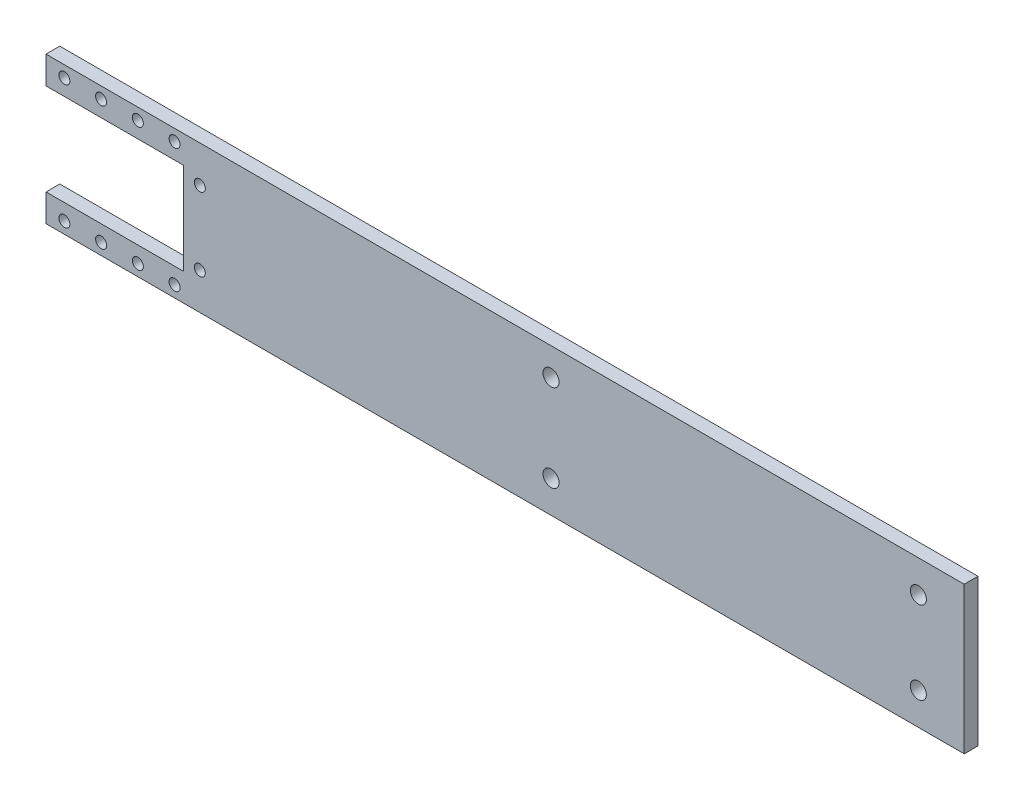
SolidWorks part; units mm, degrees
ref_plane "Front plane" through (0, 0, 0) normal (0, 0, 1) x (1, 0, 0)
ref_plane "Top plane" through (0, 0, 0) normal (0, 1, 0) x (1, 0, 0)
ref_plane "Plan de droite" through (0, 0, 0) normal (1, 0, 0) x (0, 0, -1)
sketch "Esquisse1" plane through (0, 0, 0) normal (0, 0, 1) x (1, 0, 0)
  line L0 (-12.25, 10) -> (12.25, 10)
  line L1 (19.6775, 17) -> (48.9006, -4.024)
  line L2 (48.9006, -4.024) -> (67.9013, -77.094)
  line L3 (67.9013, -77.094) -> (72.5958, -84.7726)
  line L4 (72.5958, -84.7726) -> (62.3576, -91.032)
  line L5 (62.3576, -91.032) -> (46.2854, -78.3067)
  line L6 (46.2854, -78.3067) -> (46.7112, -66.8067)
  line L7 (46.7112, -66.8067) -> (20.3918, -26.6658)
  line L8 (-12.25, 10) -> (-12.25, -10)
  line L9 (-12.25, -10) -> (12.25, -10)
  line L10 (12.25, 10) -> (12.25, -10)
  line L11 (-17.75, 10) -> (-17.75, -10)
  line L12 (-12.25, 10) -> (12.25, -10) construction
  line L13 (12.25, 10) -> (-12.25, -10) construction
  line L14 (-17.75, 10) -> (-17.75, 17)
  line L15 (-12.25, -10) -> (-17.75, -10)
  line L16 (-12.25, 10) -> (-17.75, 10)
  line L17 (44.278, -14.0621) -> (55.6029, -57.6137)
  line L18 (55.6029, -57.6137) -> (51.0231, -60.6166)
  line L19 (51.0231, -60.6166) -> (28.8161, -26.7478)
  line L20 (28.8161, -26.7478) -> (44.278, -14.0621)
  line L21 (23.25, 5.9738) -> (23.25, -19.0262)
  line L22 (23.25, -19.0262) -> (39.4851, -5.7062)
  line L23 (39.4851, -5.7062) -> (23.25, 5.9738)
  line L24 (19.6775, 17) -> (20.3918, -26.6658)
  line L25 (-1000, 0) -> (49000, 0) construction
  line L26 (-17.75, 17) -> (12.25, 17)
  line L27 (12.25, 17) -> (12.25, 10)
  line L28 (12.25, -10) -> (12.25, -16)
  line L29 (12.25, -16) -> (-17.75, -16)
  line L30 (-17.75, -16) -> (-17.75, -10)
  line L31 (19.6775, 17) -> (12.25, 17)
  line L32 (6.25, -10) -> (6.25, -16)
  line L33 (6.25, -16) -> (20.3918, -26.6658)
  point P17 (10.25, -13.5)
  point P18 (2.25, -13.5)
  point P25 (-5.75, -13.5)
  point P26 (-13.75, -13.5)
  point P27 (10.25, 13.5)
  point P28 (2.25, 13.5)
  point P29 (-5.75, 13.5)
  point P30 (-13.75, 13.5)
  point P31 (15.75, -8)
  point P32 (15.75, 8)
  dimension "D2" = 75.5
  dimension "D3" = 36
  dimension "D4" = 9
  dimension "D5" = 12
  dimension "D6" = 20.5
  dimension "D7" = 11.5
  dimension "D8" = 48
  dimension "D9" = 7
  dimension "D10" = 7
  dimension "D11" = 9.5
  dimension "D12" = 20
  dimension "D13" = 24.5
  dimension "D14" = 8
  dimension "D15" = 27
  dimension "D16" = 3.5
  dimension "D17" = 2
  dimension "D18" = 3.5
  dimension "D19" = 2
  dimension "D20" = 5.5
  dimension "D21" = 8
  dimension "D22" = 8
  dimension "D23" = 8
  dimension "D24" = 8
  dimension "D25" = 8
  dimension "D26" = 16
  dimension "D27" = 6
  dimension "D28" = 7
  dimension "D29" = 4
  dimension "D30" = 11
  dimension "D31" = 20
  dimension "D32" = 40.5
  dimension "D33" = 45
  dimension "D34" = 20
  dimension "D35" = 21
  dimension "D36" = 25
sketch "Sketch1" plane through (0, 0, 0) normal (0, 0, 1) x (1, 0, 0)
  line L13 (-17.75, 16) -> (182.25, 16)
  line L14 (-17.75, -16) -> (-17.75, -10)
  line L17 (-17.75, -10) -> (12.25, -10)
  line L18 (-17.75, 10) -> (12.25, 10)
  line L21 (-17.75, 10) -> (-17.75, 16)
  line L22 (182.25, 16) -> (182.25, -16)
  line L23 (182.25, -16) -> (-17.75, -16)
  line L24 (12.25, 10) -> (12.25, -10)
  dimension "D1" = 200
  dimension "D2" = 6
  dimension "D3" = 30
  dimension "D4" = 20
  dimension "D5" = 6
  dimension "D6" = 10
extrude "Boss-Extrude1" add sketch "Sketch1" along normal blind 3 separate body contours L13 L22 L23 L14 L17 L24 L18 L21
sketch "Sketch2" plane through (0, 0, 3) normal (0, 0, 1) x (1, 0, 0)
  line L0 (-17.168, 0) -> (29.6324, 0) construction
  point P0 (-13.75, 13.5)
  point P2 (-5.75, 13.5)
  point P4 (2.25, 13.5)
  point P6 (10.25, 13.5)
  point P8 (15.75, 8)
  point P13 (15.75, -8)
  point P14 (10.25, -13.5)
  point P15 (2.25, -13.5)
  point P16 (-5.75, -13.5)
  point P17 (-13.75, -13.5)
  dimension "D1" = 8
  dimension "D2" = 8
  dimension "D3" = 8
  dimension "D4" = 13.5
  dimension "D5" = 5.5
  dimension "D6" = 8
hole_wizard "M2 Clearance Hole1" positions "Sketch4" profile "Sketch3" hole size "M2" standard "ISO" end condition through all
sketch "Sketch4" plane through (0, 0, 3) normal (0, 0, 1) x (1, 0, 0)
  point P0 (-13.75, 13.5)
  point P3 (-5.75, 13.5)
  point P6 (2.25, 13.5)
  point P9 (10.25, 13.5)
  point P12 (15.75, 8)
  point P15 (15.75, -8)
  point P18 (10.25, -13.5)
  point P21 (2.25, -13.5)
  point P24 (-5.75, -13.5)
  point P27 (-13.75, -13.5)
sketch "Sketch3" plane through (-13.75, 13.5, 3) normal (1, 0, 0) x (0, -1, 0)
  line L0 (0, 0) -> (0, 3)
  line L1 (0, 3) -> (1.2, 3)
  line L2 (1.2, 3) -> (1.2, 0)
  line L5 (1.2, 0) -> (0, 0)
  line L11 (0, -6.35) -> (0, 107.95) construction
  dimension "Thru Hole Dia." = 2.4
  dimension "Thru Hole Depth" = 3
sketch "Sketch5" plane through (0, 0, 3) normal (0, 0, 1) x (1, 0, 0)
  line L0 (182.25, -16) -> (82.25, -16) construction
  line L1 (182.25, -16) -> (-17.75, -16) construction
  line L2 (82.25, -16) -> (82.25, 17) construction
  dimension "D1" = 100
  dimension "D2" = 33
hole_wizard "Ø3.5 (3.5) Diameter Hole1" positions "Sketch7" profile "Sketch6" hole size "Ø3.5" standard "ISO" end condition through all
sketch "Sketch7" plane through (0, 0, 3) normal (0, 0, 1) x (1, 0, 0)
  line L0 (82.25, -16) -> (82.25, 17) construction
  line L1 (182.25, 16) -> (182.25, -16) construction
  line L2 (182.25, -16) -> (82.25, -16) construction
  line L3 (-17.75, 16) -> (182.25, 16) construction
  point P0 (92.25, -9)
  point P21 (92.25, 10)
  point P23 (172.25, 9)
  point P25 (172.25, -9)
  dimension "D1" = 10
  dimension "D2" = 7
  dimension "D3" = 10
  dimension "D4" = 7
  dimension "D5" = 10
  dimension "D6" = 10
  dimension "D7" = 7
  dimension "D8" = 7
sketch "Sketch6" plane through (92.25, -9, 3) normal (1, 0, 0) x (0, -1, 0)
  line L0 (0, 0) -> (0, 3)
  line L1 (0, 3) -> (1.75, 3)
  line L2 (1.75, 3) -> (1.75, 0)
  line L5 (1.75, 0) -> (0, 0)
  line L11 (0, -6.35) -> (0, 107.95) construction
  dimension "Thru Hole Dia." = 3.5
  dimension "Thru Hole Depth" = 3
